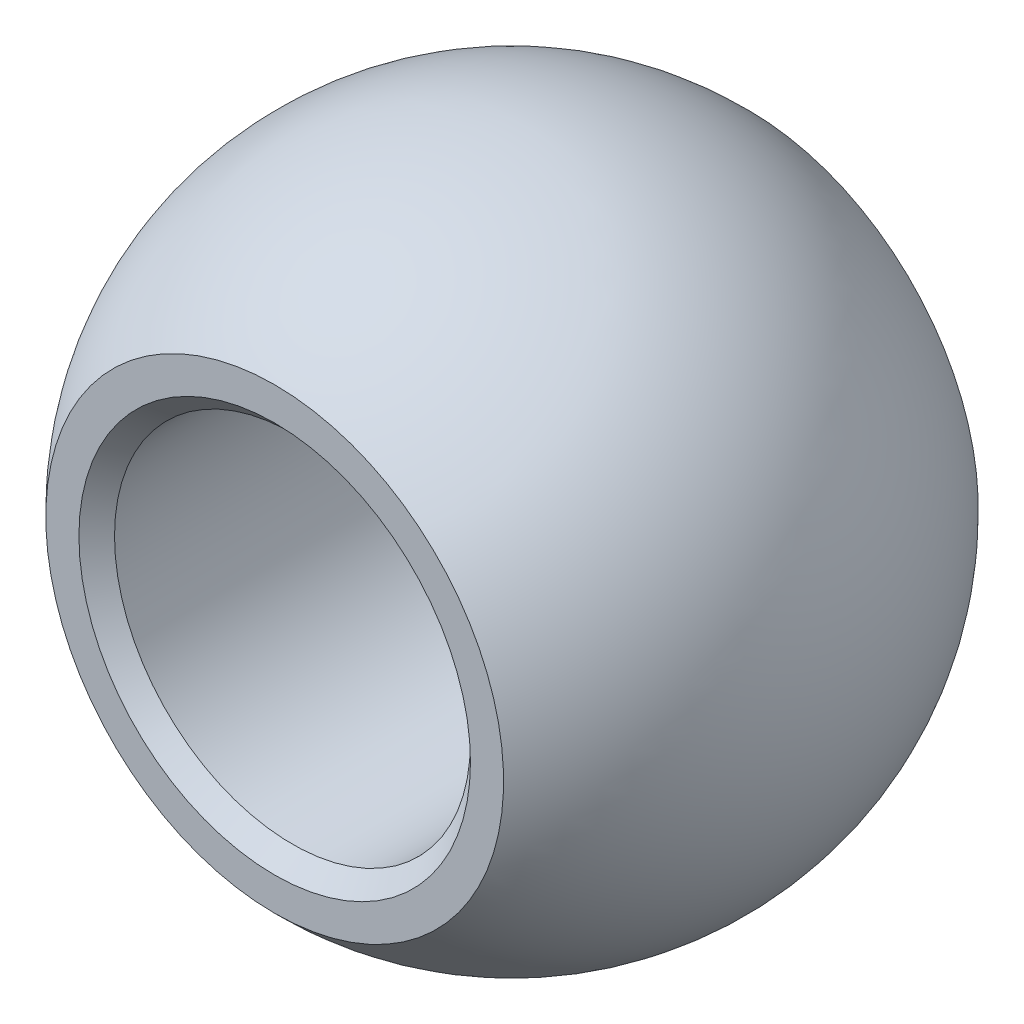
SolidWorks part; units mm, degrees
ref_plane "Front" through (0, 0, 0) normal (0, 0, 1) x (1, 0, 0)
ref_plane "Top" through (0, 0, 0) normal (0, 1, 0) x (1, 0, 0)
ref_plane "Right" through (0, 0, 0) normal (1, 0, 0) x (0, 0, -1)
sketch "Sketch1" plane through (0, 0, 0) normal (0, 0, 1) x (1, 0, 0)
  line L0 (0, -21) -> (0, -54)
  line L1 (0, -54) -> (6, -54)
  line L2 (6, -54) -> (6, -21)
  line L3 (6, -21) -> (0, -21)
  line L5 (0, 15) -> (0, -21) construction
  line L6 (0, 15) -> (15, 15) construction
  line L7 (15, 15) -> (15, 0) construction
  line L8 (-6, -54) -> (-6, -21) construction
  arc A0 (10.3448, -10.8621) -> (0, 15) centre (0, 0) ccw construction
  circle A1 centre (0, 0) radius 6 construction
  circle A2 centre (0, 0) radius 11.115 construction
  circle A3 centre (0, 0) radius 11.2261 construction
  arc A4 (6, -21) -> (10.3448, -10.8621) centre (20, -21) cw construction
  point P16 (-6, -43.9375)
  dimension "A" = 12
  dimension "Ball Dia" = 22.23
  dimension "B" = 30
  dimension "D1" = 22.4523
  dimension "D" = 54
  dimension "E" = 33
  dimension "Thread Dia" = 12
  dimension "D2" = 10.0625
sketch "Sketch4" plane through (0, 0, 0) normal (0, 0, 1) x (1, 0, 0)
  line L0 (6, -21) -> (0, -21) construction
  line L2 (0, 15) -> (0, -21) construction
  line L3 (6, -21) -> (0, -21)
  line L5 (0, 15) -> (0, -21)
  line L6 (0, 15) -> (0, 17.54) construction
  arc A0 (10.3448, -10.8621) -> (0, 15) centre (0, 0) ccw construction
  arc A1 (10.3448, -10.8621) -> (0, 15) centre (0, 0) ccw
  arc A2 (10.3448, -10.8621) -> (6, -21) centre (20, -21) ccw construction
  arc A3 (10.3448, -10.8621) -> (6, -21) centre (20, -21) ccw
  dimension "D1" = 2.54
sketch "Sketch6" plane through (0, 0, 0) normal (0, 0, 1) x (1, 0, 0)
  circle A0 centre (0, 0) radius 11.2261 construction
  circle A1 centre (0, 0) radius 11.2261
sketch "Sketch7" plane through (0, 0, 0) normal (0, 0, 1) x (1, 0, 0)
  line L0 (0, 11.115) -> (0, -11.115)
  line L1 (0, 15) -> (0, -21) construction
  line L2 (0, 0) -> (0, -11.115) construction
  arc A0 (0, -11.115) -> (0, 11.115) centre (0, 0) ccw
  circle A1 centre (0, 0) radius 11.115 construction
revolve "Revolve3" add sketch "Sketch7" angle 360 about L2
sketch "Sketch8" plane through (0, 0, 0) normal (1, 0, 0) x (0, 0, -1)
  line L1 (-8, 17.9071) -> (8, 17.9071) construction
  line L2 (-8, 17.9071) -> (-8, -17.9071)
  line L3 (-8, -17.9071) -> (8, -17.9071) construction
  line L4 (8, 17.9071) -> (8, -17.9071)
  line L5 (8, 17.9071) -> (14.8502, 17.9071)
  line L6 (14.8502, 17.9071) -> (14.8502, -17.9071)
  line L7 (14.8502, -17.9071) -> (8, -17.9071)
  line L8 (-8, -17.9071) -> (-14.8502, -17.9071)
  line L9 (-14.8502, -17.9071) -> (-14.8502, 17.9071)
  line L10 (-14.8502, 17.9071) -> (-8, 17.9071)
  line L11 (-8, -17.9071) -> (8, 17.9071) construction
  dimension "D1" = 35.8142
  dimension "C" = 16
  dimension "D2" = 6.8502
extrude "Cut-Extrude3" cut sketch "Sketch8" against normal through all and the other way through all
sketch "Sketch10" plane through (0, 0, 0) normal (0, 0, 1) x (1, 0, 0)
  circle A0 centre (0, 0) radius 6 construction
  circle A1 centre (0, 0) radius 6
extrude "Cut-Extrude4" cut sketch "Sketch10" against normal through all and the other way through all
chamfer "Chamfer1" distance 0.6 angle 45 2 edges at (6, 0, -8) (6, 0, 8)
equation "\"D1@Sketch1\"=\"Ball Dia@Sketch1\"*1.01"
equation "\"D1@Chamfer1\"=\"A@Sketch1\"/20"
